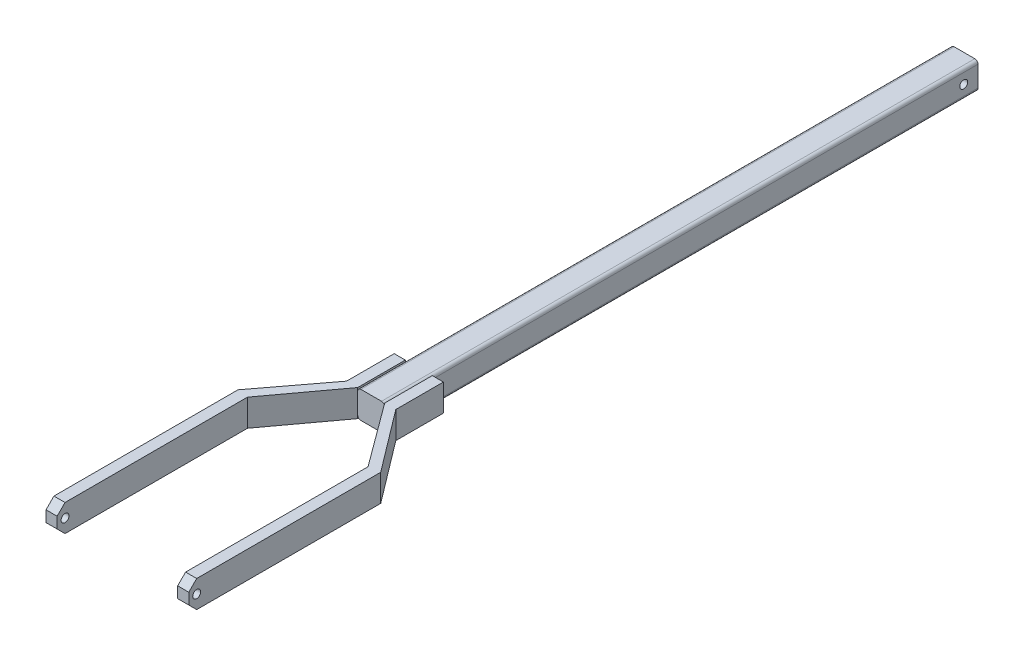
SolidWorks part; units mm, degrees
ref_plane "Front Plane" through (0, 0, 0) normal (0, 0, 1) x (1, 0, 0)
ref_plane "Top Plane" through (0, 0, 0) normal (0, 1, 0) x (1, 0, 0)
ref_plane "Right Plane" through (0, 0, 0) normal (1, 0, 0) x (0, 0, -1)
sketch "Sketch1" plane through (0, 0, 0) normal (0, 0, 1) x (1, 0, 0)
  line L1 (-38.1421, 26.9094) -> (-25.1421, 26.9094)
  line L2 (-40.1421, 24.9094) -> (-40.1421, 11.9094)
  line L3 (-38.1421, 9.9094) -> (-25.1421, 9.9094)
  line L4 (-23.1421, 24.9094) -> (-23.1421, 11.9094)
  arc A0 (-25.1421, 26.9094) -> (-23.1421, 24.9094) centre (-25.1421, 24.9094) cw
  arc A1 (-40.1421, 24.9094) -> (-38.1421, 26.9094) centre (-38.1421, 24.9094) cw
  arc A2 (-38.1421, 9.9094) -> (-40.1421, 11.9094) centre (-38.1421, 11.9094) cw
  arc A3 (-23.1421, 11.9094) -> (-25.1421, 9.9094) centre (-25.1421, 11.9094) cw
  point P6 (-23.1421, 26.9094)
  point P9 (-40.1421, 26.9094)
  point P12 (-40.1421, 9.9094)
  dimension "D3" = 2
  dimension "D1" = 17
  dimension "D2" = 17
extrude "Extrude1" add sketch "Sketch1" along normal blind 374
sketch "Sketch2" plane through (0, 26.9094, 0) normal (0, 1, 0) x (1, 0, 0)
  line L0 (-23.1421, -374) -> (-23.1421, -344)
  line L1 (-23.1421, -374) -> (-23.1421, 0) construction
  line L2 (-23.1421, -344) -> (-16.1421, -344)
  line L3 (-16.1421, -344) -> (-16.1421, -374)
  line L4 (-16.1421, -374) -> (13.3579, -413)
  line L5 (13.3579, -413) -> (13.3579, -534)
  line L6 (13.3579, -534) -> (6.3579, -534)
  line L7 (6.3579, -534) -> (6.3579, -414)
  line L8 (6.3579, -414) -> (-23.1421, -374)
  line L9 (-25.1421, 0) -> (-38.1421, 0) construction
  line L10 (-40.1421, -374) -> (-40.1421, -344)
  line L11 (-40.1421, -374) -> (-40.1421, 0) construction
  line L12 (-40.1421, -344) -> (-47.1421, -344)
  line L13 (-47.1421, -344) -> (-47.1421, -374)
  line L14 (-47.1421, -374) -> (-76.6421, -413)
  line L15 (-76.6421, -413) -> (-76.6421, -534)
  line L16 (-76.6421, -534) -> (-69.6421, -534)
  line L17 (-69.6421, -534) -> (-69.6421, -414)
  line L18 (-69.6421, -414) -> (-40.1421, -374)
  dimension "D1" = 30
  dimension "D2" = 7
  dimension "D3" = 30
  dimension "D4" = 534
  dimension "D5" = 7
  dimension "D6" = 29.5
  dimension "D7" = 7
  dimension "D8" = 534
  dimension "D9" = 7
  dimension "D10" = 120
  dimension "D11" = 121
  dimension "D12" = 121
  dimension "D13" = 120
  dimension "D14" = 30
  dimension "D15" = 30
  dimension "D16" = 29.5
extrude "Extrude2" add sketch "Sketch2" against normal blind 17
sketch "Sketch4" plane through (13.3579, 0, 0) normal (1, 0, 0) x (0, 0, -1)
  line L0 (-534, 9.9094) -> (-534, 26.9094) construction
  line L1 (0, 24.9094) -> (0, 11.9094) construction
  line L2 (-529, 26.9094) -> (-534, 21.9094)
  line L3 (-534, 26.9094) -> (-413, 26.9094) construction
  line L4 (-534, 21.9094) -> (-534, 14.9094)
  line L5 (-534, 14.9094) -> (-529, 9.9094)
  line L6 (-534, 9.9094) -> (-413, 9.9094) construction
  line L7 (-529, 9.9094) -> (-529, 0)
  line L8 (-529, 0) -> (-556.3389, 6.7204)
  line L9 (-556.3389, 6.7204) -> (-552.1411, 40.0506)
  line L10 (-552.1411, 40.0506) -> (-531.5, 37.4509)
  line L11 (-531.5, 37.4509) -> (-529, 26.9094)
  circle A0 centre (-529, 18.4094) radius 2.5
  circle A1 centre (-9, 18.4094) radius 2.5
  point P6 (0, 18.4094)
  dimension "D1" = 5
  dimension "D2" = 5
  dimension "D3" = 5
  dimension "D4" = 9
  dimension "D5" = 5
  dimension "D6" = 5
  dimension "D7" = 5
  dimension "D8" = 520
extrude "Extrude3" cut sketch "Sketch4" against normal through all
